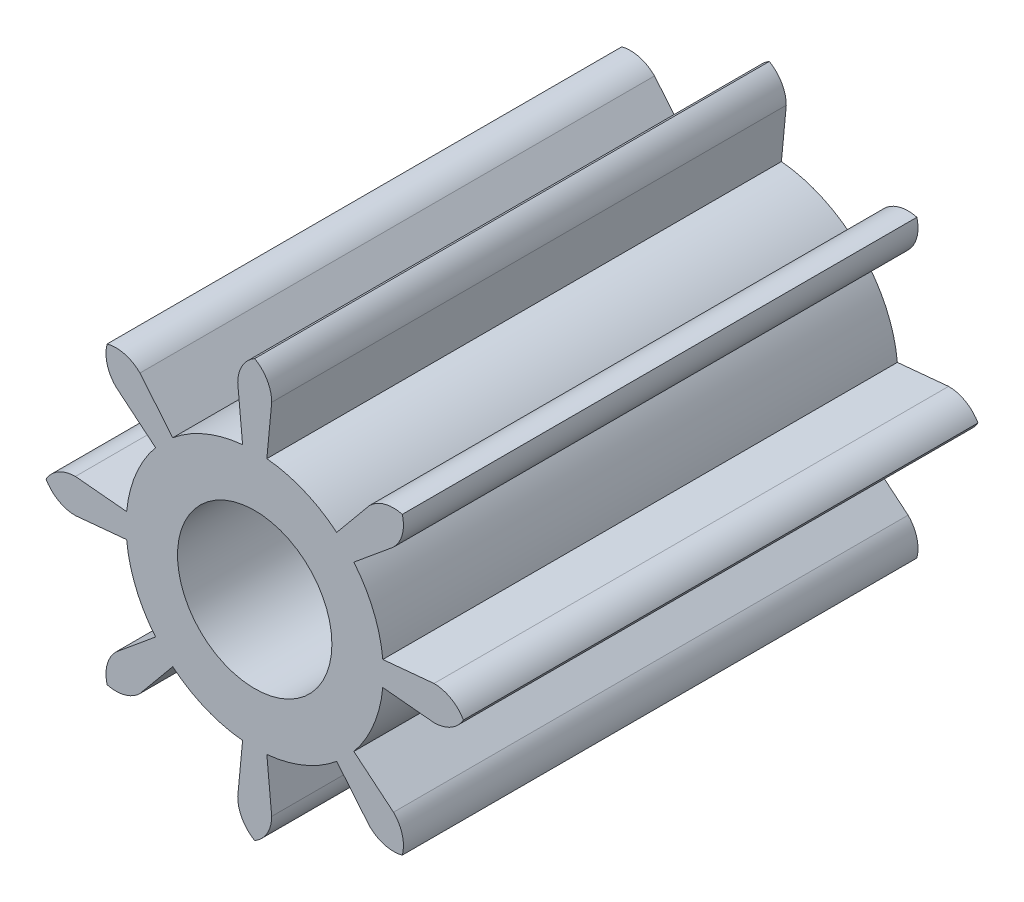
SolidWorks part; units mm, degrees
ref_plane "Front Plane" through (0, 0, 0) normal (0, 0, 1) x (1, 0, 0)
ref_plane "Top Plane" through (0, 0, 0) normal (0, 1, 0) x (1, 0, 0)
ref_plane "Right Plane" through (0, 0, 0) normal (1, 0, 0) x (0, 0, -1)
sketch "Sketch1" plane through (0, 0, 0) normal (0, 0, 1) x (1, 0, 0)
  line L0 (-0.55, 0) -> (0.55, 0) construction
  line L1 (-0.55, 0) -> (0.55, 0) construction
  line L2 (-0.33, 3.4844) -> (-0.2357, 2.4889)
  line L3 (-0.1414, 1.4933) -> (0, 0) construction
  line L4 (0, 0) -> (0.1414, 1.4933) construction
  line L5 (0.1414, 1.4933) -> (0.2357, 2.4889) construction
  line L6 (0, 4.056) -> (0, 3.5) construction
  line L7 (0, 3.5) -> (0, 2.5) construction
  line L8 (-0.2357, 2.4889) -> (-0.1414, 1.4933) construction
  line L9 (0.2357, 2.4889) -> (0.33, 3.4844)
  line L10 (-0.33, 7.0858) -> (0.33, 7.0858) construction
  circle A0 centre (0, 0) radius 3.5 construction
  arc A1 (-0.33, 3.4844) -> (0.33, 3.4844) centre (0, 0) ccw construction
  circle A2 centre (0, 0) radius 1.5
  arc A3 (0.33, 3.4844) -> (-0.33, 3.4844) centre (0, 0) ccw construction
  arc A4 (0, 4.056) -> (-0.33, 3.4844) centre (0.33, 3.4844) ccw
  arc A6 (0.33, 3.4844) -> (0, 4.056) centre (-0.33, 3.4844) ccw
  arc A7 (-0.2357, 2.4889) -> (0.2357, 2.4889) centre (0, 0) ccw
  arc A8 (0.2357, 2.4889) -> (-0.2357, 2.4889) centre (0, 0) ccw construction
  point P24 (0, 7.0858)
  dimension "D1" = 3
  dimension "D2" = 1
  dimension "D3" = 1.1
  dimension "D4" = 0.66
extrude "Boss-Extrude1" add sketch "Sketch1" against normal blind 10
pattern_circular "CirPattern1" count 8 over 360 about axis through (0, 0, 0) along (0, 0, 1) of "Boss-Extrude1"
equation "\"D4@Sketch1\"=\"D3@Sketch1\"*.6"
